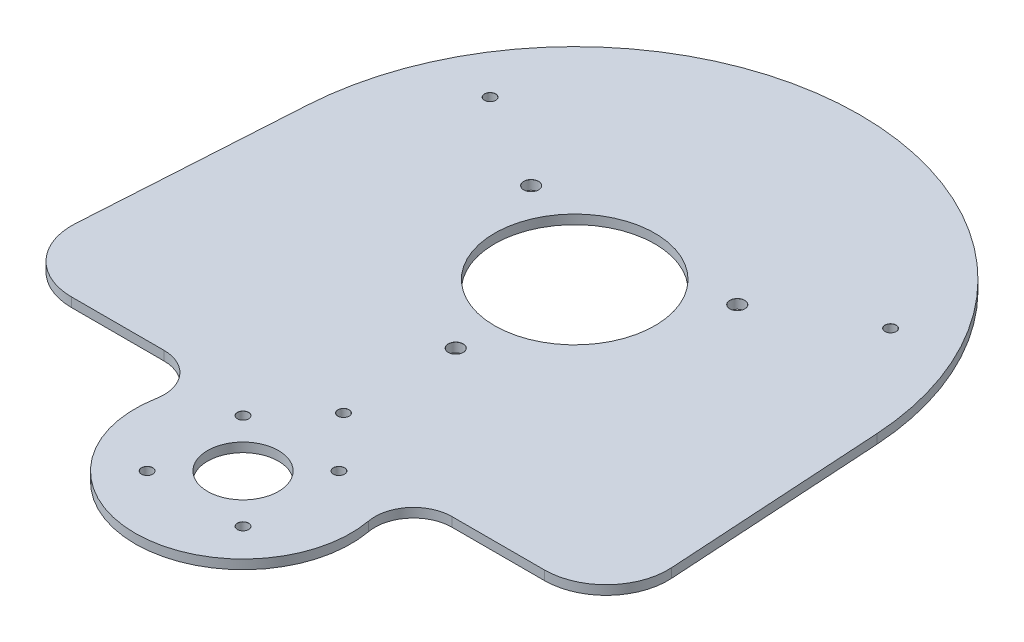
SolidWorks part; units mm, degrees
material "Thornel VCB-20 Carbon Cloth"
ref_plane "Front Plane" through (0, 0, 0) normal (0, 0, 1) x (1, 0, 0)
ref_plane "Top Plane" through (0, 0, 0) normal (0, 1, 0) x (1, 0, 0)
ref_plane "Right Plane" through (0, 0, 0) normal (1, 0, 0) x (0, 0, -1)
sketch "Sketch1" plane through (0, 0, 0) normal (0, 1, 0) x (1, 0, 0)
  line L0 (200, 147.8898) -> (200, -252.1102) construction
  line L1 (-200, -252.1102) -> (200, -252.1102) construction
  line L2 (-200, 147.8898) -> (200, 147.8898) construction
  line L3 (-200, 147.8898) -> (-200, -252.1102) construction
  line L4 (200, 147.8898) -> (200, -252.1102)
  line L5 (-200, -252.1102) -> (200, -252.1102)
  line L6 (-200, 147.8898) -> (200, 147.8898)
  line L7 (-200, 147.8898) -> (-200, -252.1102)
extrude "Boss-Extrude1" add sketch "Sketch1" against normal blind 3
ref_plane "Plane2" through (0, 0, 86.518) normal (0, 0, -1) x (-1, 0, 0)
hole_wizard "Hole1" positions "Sketch2" profile "Sketch3" legacy
sketch "Sketch2" plane through (0, 0, 0) normal (0, 1, 0) x (1, 0, 0)
  point P0 (0, 0)
sketch "Sketch3" plane through (0, 0, 0) normal (1, 0, 0) x (0, 0, 1)
  line L0 (0, 0) -> (0, 10)
  line L1 (0, 10) -> (26, 10)
  line L2 (26, 10) -> (26, 0)
  line L3 (26, 0) -> (0, 0)
  line L4 (0, 110) -> (0, -10) construction
  dimension "Diameter" = 52
  dimension "Depth" = 10
hole_wizard "Hole2" positions "Sketch4" profile "Sketch5" legacy
sketch "Sketch4" plane through (0, 0, 0) normal (0, 1, 0) x (1, 0, 0)
  point P0 (0, -107.6)
sketch "Sketch5" plane through (0, 0, 107.6) normal (1, 0, 0) x (0, 0, 1)
  line L0 (0, 0) -> (0, 100)
  line L1 (0, 100) -> (11.5, 100)
  line L2 (11.5, 100) -> (11.5, 0)
  line L3 (11.5, 0) -> (0, 0)
  line L4 (0, 110) -> (0, -10) construction
  dimension "Diameter" = 23
  dimension "Depth" = 100
sketch "Sketch6" plane through (0, 0, 0) normal (0, 1, 0) x (1, 0, 0)
  line L1 (-33.4286, 19.3) -> (0, -38.6) construction
  line L2 (0, -38.6) -> (33.4286, 19.3) construction
  line L3 (33.4286, 19.3) -> (-33.4286, 19.3) construction
  line L4 (-22, -85.6) -> (-22, -129.6) construction
  line L5 (-22, -129.6) -> (22, -129.6) construction
  line L6 (22, -129.6) -> (22, -85.6) construction
  line L7 (22, -85.6) -> (-22, -85.6) construction
  line L8 (15.5563, -92.0437) -> (-15.5563, -92.0437)
  line L9 (-15.5563, -92.0437) -> (-15.5563, -123.1563)
  line L10 (-15.5563, -123.1563) -> (15.5563, -123.1563)
  line L11 (15.5563, -123.1563) -> (15.5563, -92.0437)
  circle A0 centre (0, 0) radius 38.6 construction
  circle A1 centre (0, 0) radius 19.3 construction
  circle A2 centre (0, -107.6) radius 22 construction
  circle A3 centre (0, -107.6) radius 15.5563 construction
  point P3 (3.4038, -72.9785)
  point P8 (0, 0)
  point P21 (2.8444, -86.7887)
  point P22 (0, 0)
  dimension "D1" = 77.2
  dimension "D2" = 44
hole_wizard "M4 Clearance Hole1" positions "Sketch7" profile "Sketch8" hole size "M4" standard "ANSI Metric" end condition through all
sketch "Sketch7" plane through (0, 0, 0) normal (0, 1, 0) x (1, 0, 0)
  point P0 (0, -38.6)
  point P3 (33.4286, 19.3)
  point P6 (-33.4286, 19.3)
sketch "Sketch8" plane through (0, 0, 38.6) normal (1, 0, 0) x (0, 0, 1)
  line L0 (0, 0) -> (0, 3)
  line L1 (0, 3) -> (2.4, 3)
  line L2 (2.4, 3) -> (2.4, 0.025)
  line L3 (2.4, 0.025) -> (2.425, 0)
  line L5 (2.425, 0) -> (0, 0)
  line L6 (-2.4, 0.025) -> (-2.425, 0) construction
  line L11 (0, -6.35) -> (0, 107.95) construction
  dimension "Thru Hole Dia." = 4.8
  dimension "Thru Hole Depth" = 3
  dimension "Near C'Sink Dia." = 4.85
  dimension "Near C'Sink Angle" = 90
hole_wizard "M3 Clearance Hole1" positions "Sketch9" profile "Sketch10" hole size "M3" standard "ANSI Metric" end condition through all
sketch "Sketch9" plane through (0, 0, 0) normal (0, 1, 0) x (1, 0, 0)
  point P0 (15.5563, -92.0437)
  point P3 (-15.5563, -92.0437)
  point P6 (-15.5563, -123.1563)
  point P9 (15.5563, -123.1563)
sketch "Sketch10" plane through (15.5563, 0, 92.0437) normal (1, 0, 0) x (0, 0, 1)
  line L0 (0, 0) -> (0, 3)
  line L1 (0, 3) -> (1.8, 3)
  line L2 (1.8, 3) -> (1.8, 0.025)
  line L3 (1.8, 0.025) -> (1.825, 0)
  line L5 (1.825, 0) -> (0, 0)
  line L6 (-1.8, 0.025) -> (-1.825, 0) construction
  line L11 (0, -6.35) -> (0, 107.95) construction
  dimension "Thru Hole Dia." = 3.6
  dimension "Thru Hole Depth" = 3
  dimension "Near C'Sink Dia." = 3.65
  dimension "Near C'Sink Angle" = 90
sketch "Sketch11" plane through (0, 0, 0) normal (0, 1, 0) x (1, 0, 0)
  line L0 (-76.7183, -86.518) -> (76.7183, -86.518)
  line L1 (7.8791, -86.518) -> (-7.8791, -86.518) construction
  line L2 (96.6807, -65.293) -> (92.3263, 5.6657)
  line L3 (0, -1.65) -> (0, 1.65) construction
  line L4 (-96.6807, -65.293) -> (-92.3263, 5.6657)
  line L6 (-362.4934, 257.9992) -> (304.7529, 257.9992)
  line L7 (-362.4934, 257.9992) -> (-362.4934, -297.3891)
  line L8 (-362.4934, -297.3891) -> (304.7529, -297.3891)
  line L9 (304.7529, 257.9992) -> (304.7529, -297.3891)
  circle A0 centre (0, 0) radius 92.5
  circle A1 centre (0, -107.6) radius 35
  arc A2 (46.7183, -86.518) -> (34.424, -101.2764) centre (46.7183, -99.018) ccw
  arc A3 (-34.424, -101.2764) -> (-46.7183, -86.518) centre (-46.7183, -99.018) ccw
  circle A4 centre (76.7183, -66.518) radius 20
  circle A5 centre (-76.7183, -66.518) radius 20
  dimension "D1" = 185
  dimension "D2" = 70
  dimension "D3" = 25
  dimension "D5" = 40
  dimension "D4" = 30
extrude "Cut-Extrude1" cut sketch "Sketch11" against normal through all both and the other way through all contours L9 L6 L7 L8 L0 A5 L4 A0 L2 A4 A2 A1 A3
sketch "Sketch12" plane through (0, 0, 0) normal (0, 1, 0) x (1, 0, 0)
  line L1 (-64.9519, 37.5) -> (0, -75)
  line L2 (0, -75) -> (64.9519, 37.5)
  line L3 (64.9519, 37.5) -> (-64.9519, 37.5)
  circle A0 centre (0, 0) radius 37.5 construction
  dimension "D1" = 75
hole_wizard "M3 Clearance Hole2" positions "Sketch13" profile "Sketch14" hole size "M3" standard "ANSI Metric" end condition through all
sketch "Sketch13" plane through (0, 0, 0) normal (0, 1, 0) x (1, 0, 0)
  point P0 (-64.9519, 37.5)
  point P3 (0, -75)
  point P6 (64.9519, 37.5)
sketch "Sketch14" plane through (-64.9519, 0, -37.5) normal (1, 0, 0) x (0, 0, 1)
  line L0 (0, 0) -> (0, 3)
  line L1 (0, 3) -> (1.8, 3)
  line L2 (1.8, 3) -> (1.8, 0.025)
  line L3 (1.8, 0.025) -> (1.825, 0)
  line L5 (1.825, 0) -> (0, 0)
  line L6 (-1.8, 0.025) -> (-1.825, 0) construction
  line L11 (0, -6.35) -> (0, 107.95) construction
  dimension "Thru Hole Dia." = 3.6
  dimension "Thru Hole Depth" = 3
  dimension "Near C'Sink Dia." = 3.65
  dimension "Near C'Sink Angle" = 90
